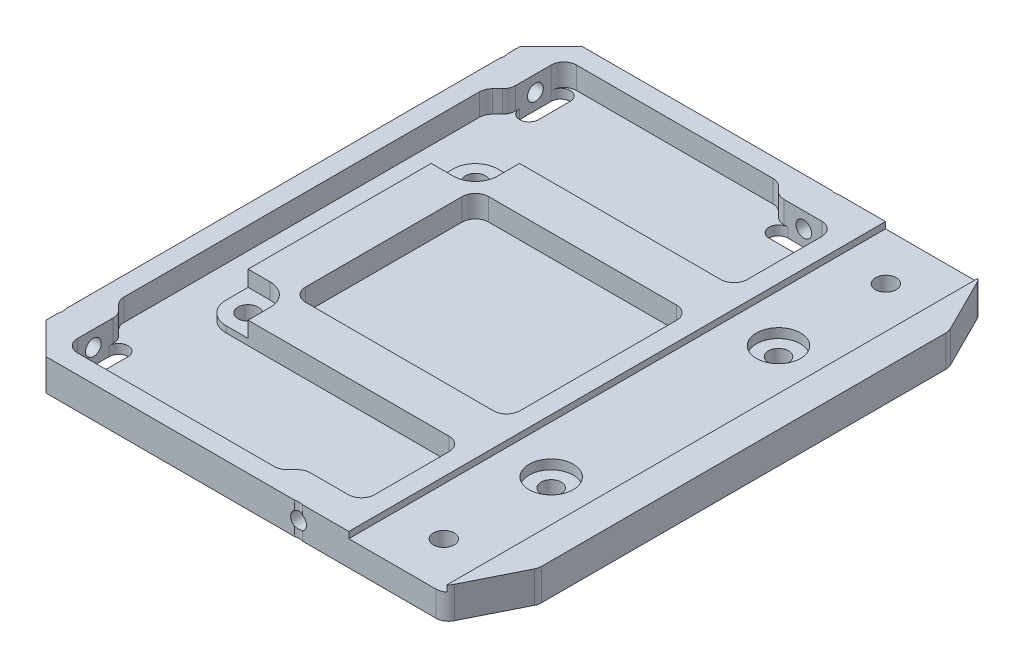
SolidWorks part; units mm, degrees
material "2014 合金"
ref_plane "正面" through (0, 0, 0) normal (0, 0, 1) x (1, 0, 0)
ref_plane "平面" through (0, 0, 0) normal (0, 1, 0) x (1, 0, 0)
ref_plane "右側面" through (0, 0, 0) normal (1, 0, 0) x (0, 0, -1)
sketch "ｽｹｯﾁ1" plane through (0, 0, 0) normal (0, 1, 0) x (1, 0, 0)
  line L1 (-36.5, -32.5) -> (36.5, -32.5) construction
  line L2 (-36.5, -32.5) -> (-36.5, 32.5)
  line L3 (-36.5, 32.5) -> (36.5, 32.5) construction
  line L4 (36.5, -32.5) -> (36.5, 32.5)
  line L5 (-36.5, -32.5) -> (36.5, 32.5) construction
  line L6 (-36.5, 32.5) -> (36.5, -32.5) construction
  line L7 (16.5, -42.5) -> (31.5, -42.5)
  line L8 (16.5, -42.5) -> (16.5, 42.5)
  line L9 (16.5, 42.5) -> (31.5, 42.5)
  line L10 (31.5, -42.5) -> (31.5, 42.5)
  line L11 (16.5, -42.5) -> (31.5, 42.5) construction
  line L12 (16.5, 42.5) -> (31.5, -42.5) construction
  line L13 (16.5, 42.5) -> (-36.5, 42.5)
  line L14 (31.5, -42.5) -> (36.5, -32.5)
  line L15 (36.5, 32.5) -> (31.5, 42.5)
  line L16 (16.5, 42.5) -> (16.5, -42.5)
  line L17 (24, 18) -> (-24, 18) construction
  line L18 (24, 18) -> (24, -18) construction
  line L19 (24, -18) -> (-24, -18) construction
  line L20 (-24, 18) -> (-24, -18) construction
  line L21 (24, 18) -> (-24, -18) construction
  line L22 (24, -18) -> (-24, 18) construction
  line L23 (16.5, -42.5) -> (-36.5, -42.5)
  line L24 (-36.5, 42.5) -> (-36.5, -42.5)
  circle A0 centre (24, -35) radius 1.65
  circle A1 centre (24, 35) radius 1.65
  circle A2 centre (-24, -18) radius 1.6
  circle A3 centre (24, -18) radius 1.6
  circle A4 centre (24, 18) radius 1.6
  circle A5 centre (-24, 18) radius 1.6
  point P0 (0, 0)
  point P6 (0, 0)
  point P18 (0, 0)
  dimension "D4" = 7.5
  dimension "D6" = 3.3
  dimension "D7" = 3.3
  dimension "D11" = 3.2
  dimension "D12" = 18
  dimension "D13" = 24
  dimension "D1" = 73
  dimension "D2" = 65
  dimension "D3" = 15
  dimension "D5" = 85
  dimension "D8" = 7.5
  dimension "D9" = 7.5
  dimension "D10" = 7.5
  dimension "D16" = 16.5
  dimension "D17" = 42.5
  dimension "D14" = 2
  dimension "D15" = 2
extrude "ﾎﾞｽ - 押し出し1" add sketch "ｽｹｯﾁ1" along normal blind 5
fillet "ﾌｨﾚｯﾄ1" radius 2 4 edges at (31.5, 2.5, -42.5) (36.5, 2.5, -32.5) (36.5, 2.5, 32.5) (31.5, 2.5, 42.5)
sketch "ｽｹｯﾁ2" plane through (0, 5, 0) normal (0, 1, 0) x (1, 0, 0)
  circle A0 centre (24, 18) radius 3.5
  circle A1 centre (24, -18) radius 3.5
  dimension "D1" = 7
  dimension "D2" = 7
extrude "ｶｯﾄ - 押し出し1" cut sketch "ｽｹｯﾁ2" against normal blind 2.5
sketch "ｽｹｯﾁ3" plane through (0, 5, 0) normal (0, 1, 0) x (1, 0, 0)
  line L0 (-36.5, 42.5) -> (30.2639, 42.5) construction
  line L1 (16.45, 42.5) -> (31.55, 42.5)
  line L2 (16.45, 42.5) -> (16.45, -42.5)
  line L3 (16.45, -42.5) -> (31.55, -42.5)
  line L4 (31.55, 42.5) -> (31.55, -42.5)
  line L5 (-36.5, -42.5) -> (30.2639, -42.5) construction
  circle A0 centre (24, 35) radius 1.65 construction
  dimension "D1" = 7.55
  dimension "D2" = 7.55
extrude "ｶｯﾄ - 押し出し2" cut sketch "ｽｹｯﾁ3" against normal blind 1
sketch "ｽｹｯﾁ4" plane through (-36.5, 0, 0) normal (-1, 0, 0) x (0, 0, 1)
  line L0 (42.5, 5) -> (-42.5, 5) construction
  circle A0 centre (-35, 2.5) radius 1.25
  circle A1 centre (35, 2.5) radius 1.25
  dimension "D3" = 2.5
  dimension "D4" = 2.5
  dimension "D5" = 2.5
  dimension "D6" = 35
  dimension "D1" = 35
  dimension "D2" = 2.5
extrude "ｶｯﾄ - 押し出し3" cut sketch "ｽｹｯﾁ4" against normal blind 5
chamfer "面取り1" distance 5 angle 45 2 edges at (-36.5, 2.5, 42.5) (-36.5, 2.5, -42.5)
sketch "ｽｹｯﾁ6" plane through (0, 0, 42.5) normal (0, 0, 1) x (1, 0, 0)
  line L0 (-36.5, 0) -> (-36.5, 5) construction
  line L1 (30.2639, 0) -> (-31.5, 0) construction
  circle A0 centre (8.5, 2.5) radius 1.25
  dimension "D1" = 45
  dimension "D2" = 2.5
  dimension "D3" = 2.5
extrude "ｶｯﾄ - 押し出し5" cut sketch "ｽｹｯﾁ6" against normal blind 5
sketch "ｽｹｯﾁ7" plane through (0, 0, -42.5) normal (0, 0, -1) x (-1, 0, 0)
  line L0 (36.5, 5) -> (36.5, 0) construction
  line L1 (-30.2639, 0) -> (31.5, 0) construction
  circle A0 centre (-8.5, 2.5) radius 1.25
  dimension "D1" = 45
  dimension "D2" = 2.5
  dimension "D3" = 2.5
extrude "ｶｯﾄ - 押し出し6" cut sketch "ｽｹｯﾁ7" against normal blind 5
sketch "ｽｹｯﾁ5" plane through (0, 5, 0) normal (0, 1, 0) x (1, 0, 0)
  line L0 (-36.5, -37.5) -> (-36.5, 37.5) construction
  line L1 (16.45, 42.5) -> (-31.5, 42.5) construction
  line L2 (16.45, -42.5) -> (-31.5, -42.5) construction
  line L3 (-36.5, 37.5) -> (-36.5, -37.5) construction
  circle A0 centre (-38.5, 35) radius 2.1
  circle A1 centre (-38.5, -35) radius 2.1
  circle A2 centre (8.5, -44.5) radius 2.1
  circle A3 centre (8.5, 44.5) radius 2.1
  dimension "D1" = 4.2
  dimension "D3" = 35
  dimension "D5" = 4.2
  dimension "D9" = 4.2
  dimension "D10" = 4.2
  dimension "D11" = 45
  dimension "D12" = 45
  dimension "D2" = 2
  dimension "D4" = 2
  dimension "D6" = 35
  dimension "D7" = 2
  dimension "D8" = 2
extrude "ｶｯﾄ - 押し出し4" cut sketch "ｽｹｯﾁ5" against normal through all
sketch "ｽｹｯﾁ8" plane through (0, 5, 0) normal (0, 1, 0) x (1, 0, 0)
  line L0 (-20.5, 18) -> (-20.5, 21.5)
  line L1 (-20.5, 21.5) -> (-24, 21.5)
  line L2 (-27.5, 18) -> (-27.5, 14.5)
  line L3 (-27.5, 14.5) -> (-24, 14.5)
  line L4 (-27.5, -18) -> (-27.5, -14.5)
  line L5 (-27.5, -14.5) -> (-24, -14.5)
  line L6 (-24, -21.5) -> (-20.5, -21.5)
  line L7 (-20.5, -21.5) -> (-20.5, -18)
  arc A0 (-24, 21.5) -> (-27.5, 18) centre (-24, 18) ccw
  arc A1 (-27.5, -18) -> (-24, -21.5) centre (-24, -18) ccw
  arc A2 (-24, 14.5) -> (-20.5, 18) centre (-24, 18) ccw
  arc A3 (-20.5, -18) -> (-24, -14.5) centre (-24, -18) ccw
  dimension "D1" = 7
extrude "ｶｯﾄ - 押し出し7" cut sketch "ｽｹｯﾁ8" against normal blind 2.5
sketch "ｽｹｯﾁ10" plane through (0, 5, 0) normal (0, 1, 0) x (1, 0, 0)
  line L0 (-36.5, 0) -> (36.5, 0) construction
  line L5 (-30, 32.5) -> (-30, 37.5) construction
  line L6 (-31.5, 32.5) -> (-31.5, 37.5)
  line L11 (16.45, 42.5) -> (9.1403, 42.5) construction
  line L12 (-36.5, 37.5) -> (-36.5, 35.6403) construction
  line L17 (-36.5, 34.3597) -> (-36.5, -34.3597) construction
  line L18 (36.5, -32.0279) -> (36.5, 32.0279) construction
  line L25 (6, 36) -> (11, 36) construction
  line L26 (6, 37.5) -> (11, 37.5)
  line L27 (6, 34.5) -> (11, 34.5)
  line L28 (-28.5, 32.5) -> (-28.5, 37.5)
  line L29 (6, -36) -> (11, -36) construction
  line L30 (6, -37.5) -> (11, -37.5)
  line L31 (6, -34.5) -> (11, -34.5)
  line L32 (-30, -32.5) -> (-30, -37.5) construction
  line L33 (-31.5, -32.5) -> (-31.5, -37.5)
  line L34 (-28.5, -32.5) -> (-28.5, -37.5)
  arc A0 (7.8597, 42.5) -> (9.1403, 42.5) centre (8.5, 44.5) ccw construction
  arc A2 (6, 37.5) -> (6, 34.5) centre (6, 36) ccw
  arc A3 (11, 34.5) -> (11, 37.5) centre (11, 36) ccw
  arc A4 (-31.5, 32.5) -> (-28.5, 32.5) centre (-30, 32.5) ccw
  arc A5 (-28.5, 37.5) -> (-31.5, 37.5) centre (-30, 37.5) ccw
  arc A6 (-36.5, 34.3597) -> (-36.5, 35.6403) centre (-38.5, 35) ccw construction
  arc A7 (6, -37.5) -> (6, -34.5) centre (6, -36) cw
  arc A8 (11, -34.5) -> (11, -37.5) centre (11, -36) cw
  arc A9 (-31.5, -32.5) -> (-28.5, -32.5) centre (-30, -32.5) cw
  arc A10 (-28.5, -37.5) -> (-31.5, -37.5) centre (-30, -37.5) cw
  point P2 (-30, 35)
  point P8 (-36.4, 35)
  point P9 (-31.5, 35)
  point P19 (8.5, 42.4)
  point P22 (8.5, 37.5)
  point P29 (8.5, -36)
  point P32 (8.5, 36)
  point P43 (-30, -35)
  dimension "D1" = 5
  dimension "D2" = 3
  dimension "D3" = 5
  dimension "D4" = 5
  dimension "D7" = 5
  dimension "D8" = 3
extrude "ｶｯﾄ - 押し出し9" cut sketch "ｽｹｯﾁ10" against normal through all
sketch "ｽｹｯﾁ9" plane through (0, 5, 0) normal (0, 1, 0) x (1, 0, 0)
  line L0 (-20.5, -14.5) -> (13.45, -14.5)
  line L1 (-24, 18) -> (24, 18) construction
  line L2 (-24, 18) -> (-24, -18) construction
  line L3 (-24, -18) -> (24, -18) construction
  line L4 (24, 18) -> (24, -18) construction
  line L5 (-20.5, 14.5) -> (-20.5, -14.5)
  line L6 (-20.5, 14.5) -> (13.45, 14.5)
  line L7 (13.45, 14.5) -> (13.45, -14.5)
  line L8 (16.45, 42.5) -> (16.45, -42.5) construction
  line L9 (-20.5, 14.5) -> (24, 14.5) construction
  line L10 (-20.5, -14.5) -> (24, -14.5) construction
  line L14 (-24, 21.5) -> (13.45, 21.5)
  line L15 (13.45, 34.5) -> (13.45, 21.5)
  line L16 (7.8597, 42.5) -> (-31.5, 42.5) construction
  line L17 (-27.5, 18) -> (-27.5, -18)
  line L19 (-36.5, 0) -> (16.45, 0) construction
  line L22 (-36.5, 34.3597) -> (-36.5, -34.3597) construction
  line L23 (-33.5, 29) -> (-33.5, -29)
  line L26 (2.5, 39.5) -> (-31.5, 39.5)
  line L45 (-31.5, 32.5) -> (-31.5, 31)
  line L46 (6, 37.5) -> (4.5, 37.5)
  line L49 (11, 37.5) -> (6, 37.5) construction
  line L50 (-31.5, 37.5) -> (-31.5, 32.5) construction
  line L51 (11, 37.5) -> (6, 37.5)
  line L52 (-31.5, 37.5) -> (-31.5, 32.5)
  line L59 (-24, -21.5) -> (13.45, -21.5)
  line L60 (13.45, -34.5) -> (13.45, -21.5)
  line L66 (11, -37.5) -> (6, -37.5)
  line L67 (6, -37.5) -> (4.5, -37.5)
  line L72 (-31.5, -37.5) -> (-31.5, -32.5)
  line L73 (-31.5, -32.5) -> (-31.5, -31)
  line L78 (-31.5, 37.5) -> (-31.5, 39.5)
  line L79 (13.45, 34.5) -> (13.45, 37.5)
  line L80 (13.45, 37.5) -> (11, 37.5)
  line L81 (4.5, 37.5) -> (2.5, 39.5)
  line L82 (-31.5, 31) -> (-33.5, 29)
  line L83 (13.45, -34.5) -> (13.45, -37.5)
  line L84 (13.45, -37.5) -> (11, -37.5)
  line L85 (4.5, -37.5) -> (2.5, -39.5)
  line L86 (2.5, -39.5) -> (-31.5, -39.5)
  line L87 (-31.5, -37.5) -> (-31.5, -39.5)
  line L88 (-31.5, -31) -> (-33.5, -29)
  circle A0 centre (-24, 18) radius 3.5 construction
  circle A4 centre (-24, 18) radius 3.5 construction
  arc A19 (-24, 21.5) -> (-27.5, 18) centre (-24, 18) ccw
  arc A20 (-24, -21.5) -> (-27.5, -18) centre (-24, -18) cw
  arc A21 (6, 37.5) -> (6, 34.5) centre (6, 36) ccw construction
  arc A22 (-31.5, 32.5) -> (-28.5, 32.5) centre (-30, 32.5) ccw construction
  point P4 (0, 0)
  point P29 (0, 0)
  point P30 (-27.5, 0)
  point P31 (-27.5, 0)
  point P56 (-33.5, 0)
  point P59 (4.5, 36)
  point P60 (-33.5, 0)
  point P64 (-30, 31)
  dimension "D2" = 3
  dimension "D3" = 3
  dimension "D4" = 3
  dimension "D5" = 3
  dimension "D1" = 135
  dimension "D6" = 135
extrude "ｶｯﾄ - 押し出し8" cut sketch "ｽｹｯﾁ9" against normal blind 3.5
fillet "ﾌｨﾚｯﾄ29" radius 2.1 16 edges at (13.45, 3.25, -37.5) (13.45, 3.25, -21.5) (-33.5, 3.25, -29) (2.5, 3.25, 39.5) (-33.5, 3.25, 29) (13.45, 3.25, 21.5) (13.45, 3.25, 37.5) (4.5, 3.25, 37.5) (-31.5, 3.25, 31) (-31.5, 3.25, -31) (4.5, 3.25, -37.5) (2.5, 3.25, -39.5) (13.45, 3.25, -14.5) (-20.5, 3.25, -14.5) (-20.5, 3.25, 14.5) (13.45, 3.25, 14.5)
fillet "ﾌｨﾚｯﾄ30" radius 2 2 edges at (-31.5, 3.25, 39.5) (-31.5, 3.25, -39.5)
